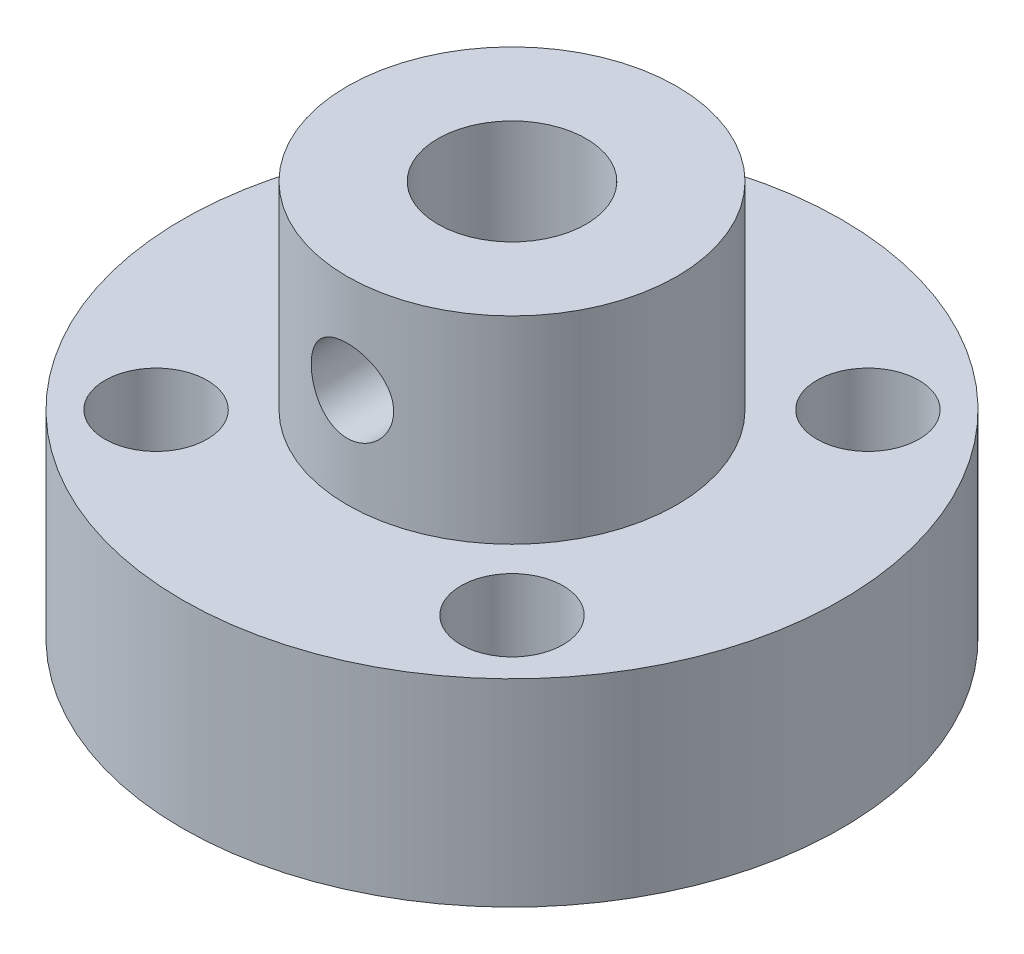
SolidWorks part; units mm, degrees
ref_plane "Ebene vorne" through (0, 0, 0) normal (0, 0, 1) x (1, 0, 0)
ref_plane "Ebene oben" through (0, 0, 0) normal (0, 1, 0) x (1, 0, 0)
ref_plane "Ebene rechts" through (0, 0, 0) normal (1, 0, 0) x (0, 0, -1)
sketch "Skizze1" plane through (0, 0, 0) normal (0, 1, 0) x (1, 0, 0)
  circle A0 centre (0, 0) radius 10
  dimension "D1" = 20
extrude "Aufsatz-Linear austragen1" add sketch "Skizze1" along normal blind 6
sketch "Skizze2" plane through (0, 6, 0) normal (0, 1, 0) x (1, 0, 0)
  circle A0 centre (0, 0) radius 5
  dimension "D1" = 10
extrude "Aufsatz-Linear austragen2" add sketch "Skizze2" along normal blind 6
sketch "Skizze3" plane through (0, 12, 0) normal (0, 1, 0) x (1, 0, 0)
  circle A0 centre (0, 0) radius 2.25
  dimension "D1" = 4.5
extrude "Schnitt-Linear austragen1" cut sketch "Skizze3" against normal blind 9
sketch "Skizze4" plane through (0, 6, 0) normal (0, 1, 0) x (1, 0, 0)
  line L1 (-5.4, 5.4) -> (5.4, 5.4) construction
  line L2 (-5.4, 5.4) -> (-5.4, -5.4) construction
  line L3 (-5.4, -5.4) -> (5.4, -5.4) construction
  line L4 (5.4, 5.4) -> (5.4, -5.4) construction
  line L5 (-5.4, 5.4) -> (5.4, -5.4) construction
  line L6 (-5.4, -5.4) -> (5.4, 5.4) construction
  circle A0 centre (-5.4, 5.4) radius 1.55
  circle A1 centre (5.4, 5.4) radius 1.55
  circle A2 centre (5.4, -5.4) radius 1.55
  circle A3 centre (-5.4, -5.4) radius 1.55
  point P0 (0, 0)
  dimension "D2" = 3.1
  dimension "D1" = 10.8
extrude "Schnitt-Linear austragen2" cut sketch "Skizze4" against normal through all
ref_plane "Ebene1" through (0, 0, 5) normal (0, 0, 1) x (1, 0, 0)
sketch "Skizze5" plane through (0, 0, 5) normal (0, 0, 1) x (1, 0, 0)
  line L0 (0, 12) -> (0, 6) construction
  line L1 (2.25, 12) -> (-2.25, 12) construction
  line L2 (10, 6) -> (-10, 6) construction
  circle A0 centre (0, 9) radius 1.25
  dimension "D1" = 2.5
  dimension "D2" = 3
extrude "Schnitt-Linear austragen3" cut sketch "Skizze5" against normal up to next
